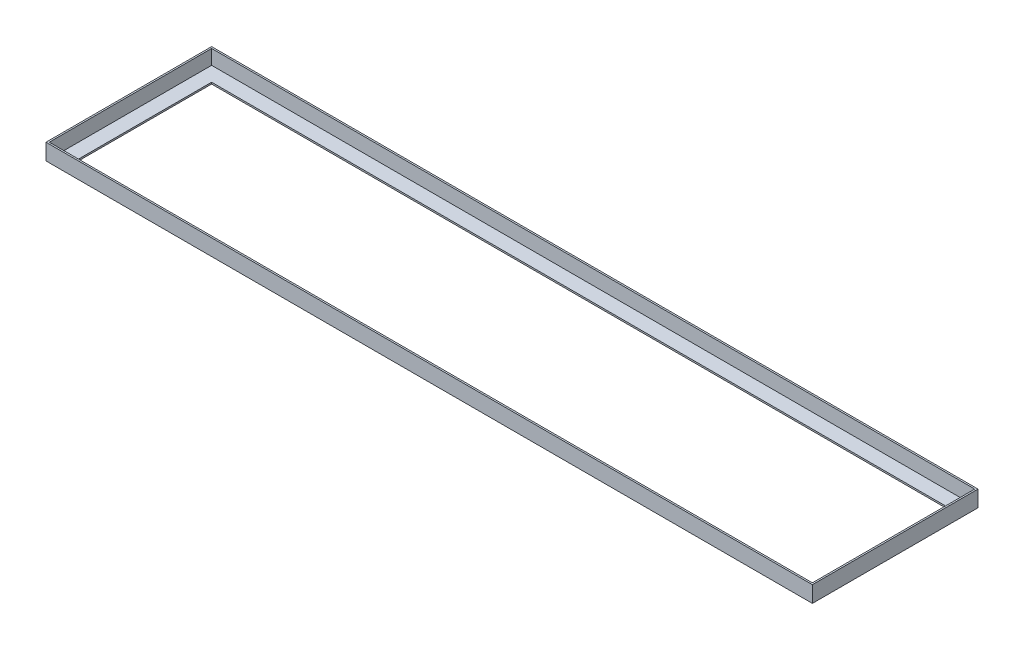
SolidWorks part; units mm, degrees
material "AISI 1020"
ref_plane "Front Plane" through (0, 0, 0) normal (0, 0, 1) x (1, 0, 0)
ref_plane "Top Plane" through (0, 0, 0) normal (0, 1, 0) x (1, 0, 0)
ref_plane "Right Plane" through (0, 0, 0) normal (1, 0, 0) x (0, 0, -1)
sketch "Sketch1" plane through (0, 0, 0) normal (0, 0, 1) x (1, 0, 0)
  line L1 (-78.9001, 15.665) -> (865.0999, 15.665)
  line L2 (-78.9001, 15.665) -> (-78.9001, -4.335)
  line L3 (-78.9001, -4.335) -> (865.0999, -4.335)
  line L4 (865.0999, 15.665) -> (865.0999, -4.335)
  dimension "D1" = 20
  dimension "D2" = 944
extrude "Boss-Extrude1" add sketch "Sketch1" against normal blind 204
sketch3d "3DSketch1"
  line L0 (863.0999, 15.665, -202) -> (-76.9001, 15.665, -202)
  line L1 (-76.9001, 15.665, -202) -> (-76.9001, 15.665, -2)
  line L2 (863.0999, 15.665, -2) -> (-76.9001, 15.665, -2)
  line L3 (863.0999, 15.665, -202) -> (863.0999, 15.665, -2)
  line L4 (863.0999, 15.665, -202) -> (-76.9001, 15.665, -202)
  line L5 (-76.9001, 15.665, -202) -> (-76.9001, 15.665, -2)
  line L6 (863.0999, 15.665, -2) -> (-76.9001, 15.665, -2)
  line L7 (863.0999, 15.665, -202) -> (863.0999, 15.665, -2)
  dimension "D1" = 2
extrude "Cut-Extrude1" cut sketch "3DSketch1" along direction (0, 1, 0) on the side of the normal blind 18
sketch3d "3DSketch2"
  line L0 (-58.9001, -2.335, -184) -> (845.0999, -2.335, -184)
  line L1 (-58.9001, -2.335, -20) -> (-58.9001, -2.335, -184)
  line L2 (845.0999, -2.335, -20) -> (-58.9001, -2.335, -20)
  line L3 (845.0999, -2.335, -184) -> (845.0999, -2.335, -20)
  line L4 (-58.9001, -2.335, -184) -> (845.0999, -2.335, -184)
  line L5 (-58.9001, -2.335, -20) -> (-58.9001, -2.335, -184)
  line L6 (845.0999, -2.335, -20) -> (-58.9001, -2.335, -20)
  line L7 (845.0999, -2.335, -184) -> (845.0999, -2.335, -20)
  dimension "D1" = 18
extrude "Cut-Extrude2" cut sketch "3DSketch2" along direction (0, -1, 0) on the side of the normal blind 2
